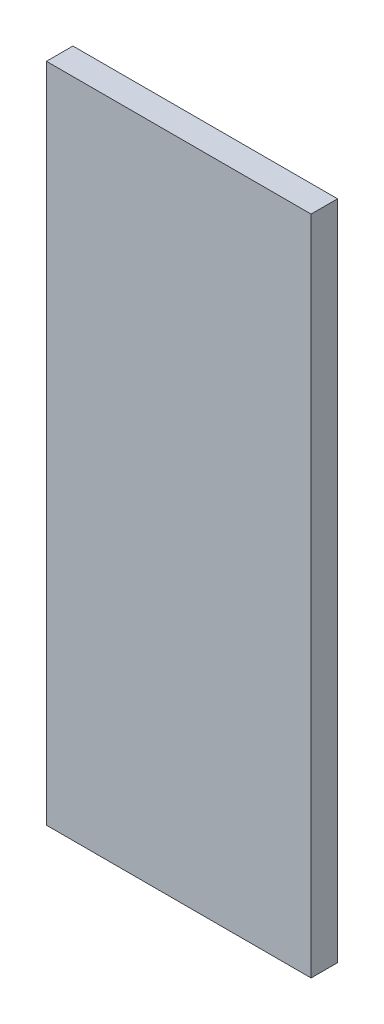
SolidWorks part; units mm, degrees
ref_plane "Спереди" through (0, 0, 0) normal (0, 0, 1) x (1, 0, 0)
ref_plane "Сверху" through (0, 0, 0) normal (0, 1, 0) x (1, 0, 0)
ref_plane "Справа" through (0, 0, 0) normal (1, 0, 0) x (0, 0, -1)
sketch "Эскиз1" plane through (0, 0, 0) normal (0, 1, 0) x (1, 0, 0)
  line L1 (0, 0) -> (20, 0)
  line L2 (0, 0) -> (0, 2)
  line L3 (0, 2) -> (20, 2)
  line L4 (20, 0) -> (20, 2)
extrude "Бобышка-Вытянуть1" add sketch "Эскиз1" along normal blind 50
